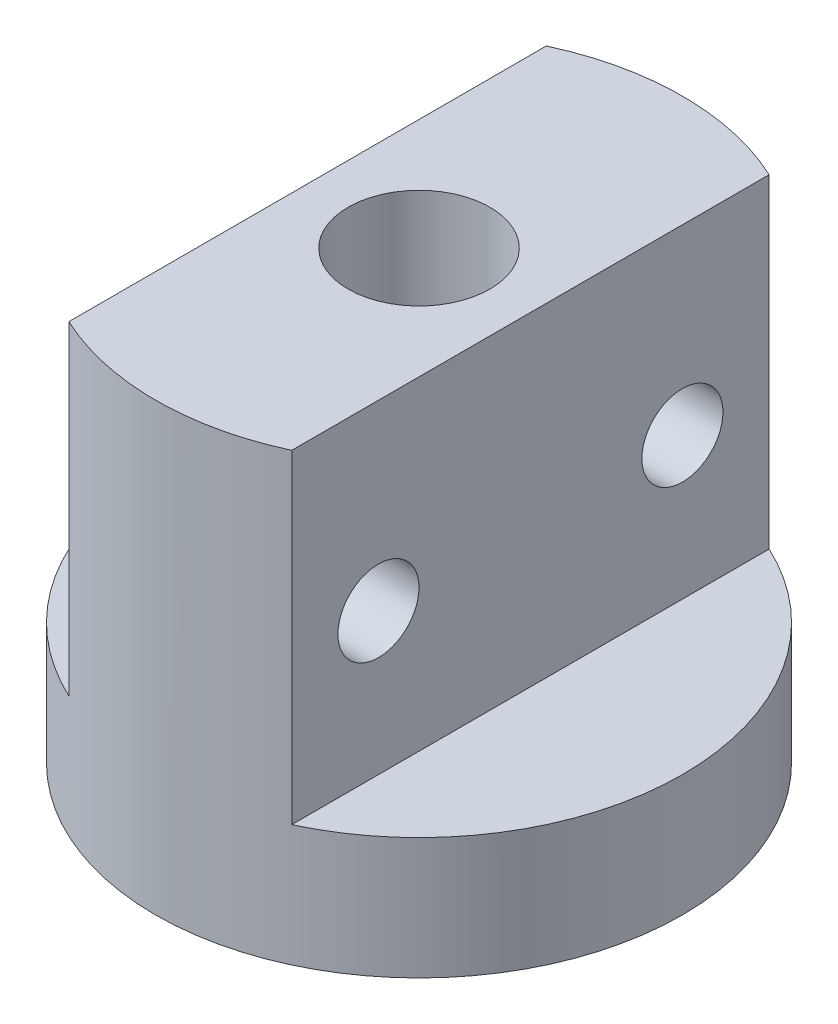
SolidWorks part; units mm, degrees
ref_plane "Front Plane" through (0, 0, 0) normal (0, 0, 1) x (1, 0, 0)
ref_plane "Top Plane" through (0, 0, 0) normal (0, 1, 0) x (1, 0, 0)
ref_plane "Right Plane" through (0, 0, 0) normal (1, 0, 0) x (0, 0, -1)
sketch "Sketch1" plane through (0, 0, 0) normal (0, 1, 0) x (1, 0, 0)
  circle A0 centre (0, 0) radius 13
  dimension "D1" = 26
extrude "Boss-Extrude1" add sketch "Sketch1" along normal blind 22
sketch "Sketch2" plane through (0, 0, 0) normal (0, 1, 0) x (1, 0, 0)
  circle A0 centre (0, 0) radius 7
  dimension "D1" = 14
extrude "Cut-Extrude1" cut sketch "Sketch2" along normal blind 5
sketch "Sketch3" plane through (0, 0, 0) normal (0, 0, 1) x (1, 0, 0)
  line L1 (14.2097, 23.8611) -> (5.5, 23.8611)
  line L2 (14.2097, 23.8611) -> (14.2097, 6)
  line L3 (14.2097, 6) -> (5.5, 6)
  line L4 (5.5, 23.8611) -> (5.5, 6)
  line L5 (-14.5323, 23.8025) -> (-5.5, 23.8025)
  line L6 (-14.5323, 23.8025) -> (-14.5323, 6)
  line L7 (-14.5323, 6) -> (-5.5, 6)
  line L8 (-5.5, 23.8025) -> (-5.5, 6)
  dimension "D1" = 16
  dimension "D2" = 16
  dimension "D3" = 7.5
  dimension "D4" = 7.5
extrude "Cut-Extrude2" cut sketch "Sketch3" against normal through all and the other way through all
sketch "Sketch4" plane through (0, 0, 0) normal (1, 0, 0) x (0, 0, -1)
  line L0 (-18.0224, 13) -> (16.644, 13) construction
  line L1 (0, -2.6031) -> (0, 24.7862) construction
  circle A0 centre (-7.5, 13) radius 2
  circle A1 centre (7.5, 13) radius 2
  dimension "D1" = 4
  dimension "D2" = 4
  dimension "D3" = 9
  dimension "D4" = 7.5
  dimension "D5" = 7.5
extrude "Cut-Extrude3" cut sketch "Sketch4" against normal through all and the other way through all
sketch "Sketch5" plane through (0, 0, 0) normal (0, 1, 0) x (1, 0, 0)
  circle A0 centre (0, 0) radius 3.5
extrude "Cut-Extrude4" cut sketch "Sketch5" against normal blind 5 from surface at 22 starting at face at (0, 22, 0)
sketch "Sketch6" plane through (0, 0, 0) normal (0, 1, 0) x (1, 0, 0)
  circle A0 centre (0, 0) radius 1.5
extrude "Cut-Extrude5" cut sketch "Sketch6" along normal through all
